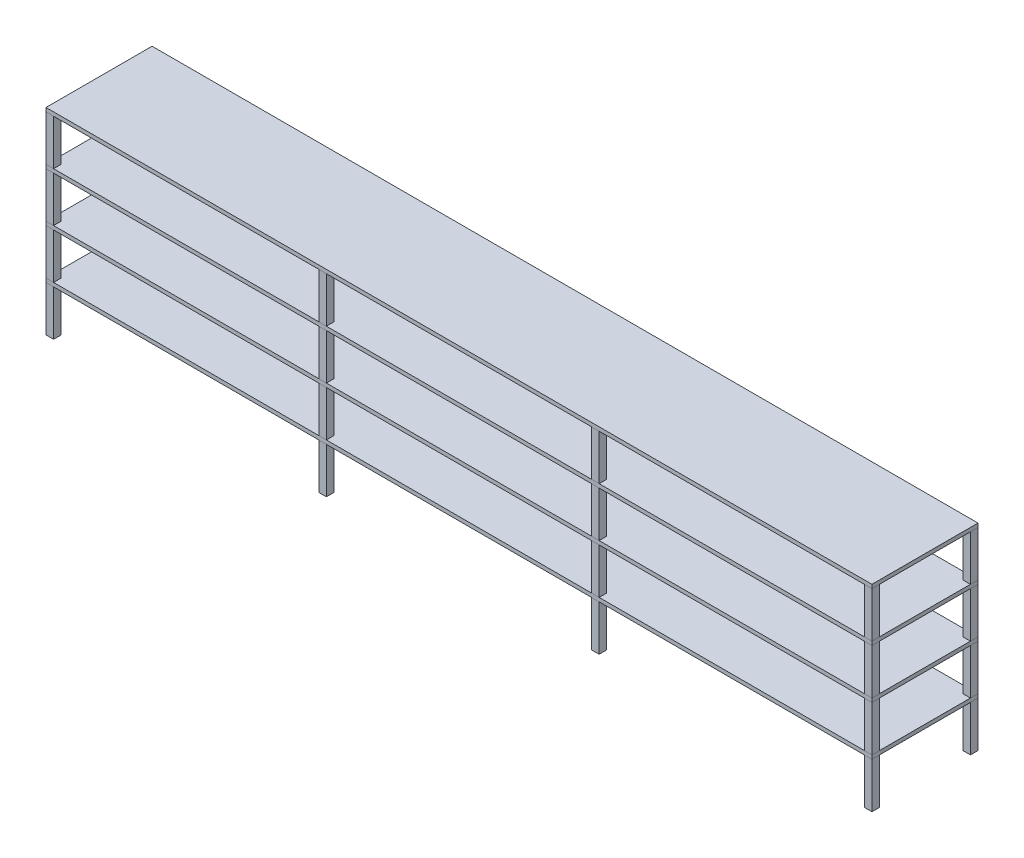
SolidWorks part; units mm, degrees
material "6061 Alloy"
ref_plane "Front Plane" through (0, 0, 0) normal (0, 0, 1) x (1, 0, 0)
ref_plane "Top Plane" through (0, 0, 0) normal (0, 1, 0) x (1, 0, 0)
ref_plane "Right Plane" through (0, 0, 0) normal (1, 0, 0) x (0, 0, -1)
sketch "Sketch1" plane through (0, 0, 0) normal (0, 1, 0) x (1, 0, 0)
  line L1 (-346.075, -44.45) -> (346.075, -44.45)
  line L2 (-346.075, -44.45) -> (-346.075, 44.45)
  line L3 (-346.075, 44.45) -> (346.075, 44.45)
  line L4 (346.075, -44.45) -> (346.075, 44.45)
  line L5 (-346.075, -44.45) -> (346.075, 44.45) construction
  line L6 (-346.075, 44.45) -> (346.075, -44.45) construction
  point P0 (0, 0)
  dimension "D1" = 88.9
  dimension "D2" = 692.15
sketch "Sketch2" plane through (0, 0, 0) normal (0, 1, 0) x (1, 0, 0)
  line L0 (-117.475, 44.45) -> (-117.475, 38.1)
  line L1 (-346.075, -44.45) -> (-339.725, -44.45)
  line L2 (-346.075, 44.45) -> (-339.725, 44.45)
  line L3 (-346.075, 44.45) -> (-346.075, 38.1)
  line L4 (-346.075, 38.1) -> (-339.725, 38.1)
  line L5 (-339.725, 44.45) -> (-339.725, 38.1)
  line L6 (-346.075, -44.45) -> (-346.075, -38.1)
  line L7 (-346.075, -38.1) -> (-339.725, -38.1)
  line L8 (-339.725, -44.45) -> (-339.725, -38.1)
  line L9 (-117.475, 44.45) -> (-111.125, 44.45)
  line L10 (-111.125, 44.45) -> (-111.125, 38.1)
  line L11 (-117.475, 38.1) -> (-111.125, 38.1)
  line L12 (-117.475, -38.1) -> (-111.125, -38.1)
  line L13 (-117.475, -44.45) -> (-117.475, -38.1)
  line L14 (-111.125, -44.45) -> (-111.125, -38.1)
  line L15 (-117.475, -44.45) -> (-111.125, -44.45)
  line L16 (111.125, 44.45) -> (111.125, 38.1)
  line L17 (111.125, 44.45) -> (117.475, 44.45)
  line L18 (117.475, 44.45) -> (117.475, 38.1)
  line L19 (111.125, 38.1) -> (117.475, 38.1)
  line L20 (111.125, -38.1) -> (117.475, -38.1)
  line L21 (111.125, -44.45) -> (111.125, -38.1)
  line L22 (117.475, -44.45) -> (117.475, -38.1)
  line L23 (111.125, -44.45) -> (117.475, -44.45)
  line L24 (339.725, 44.45) -> (339.725, 38.1)
  line L25 (339.725, 44.45) -> (346.075, 44.45)
  line L26 (346.075, 44.45) -> (346.075, 38.1)
  line L27 (339.725, 38.1) -> (346.075, 38.1)
  line L28 (339.725, -38.1) -> (346.075, -38.1)
  line L29 (339.725, -44.45) -> (339.725, -38.1)
  line L30 (346.075, -44.45) -> (346.075, -38.1)
  line L31 (339.725, -44.45) -> (346.075, -44.45)
  dimension "D1" = 6.35
extrude "Extrude1" add sketch "Sketch2" along normal blind 38.1
sketch "Sketch3" plane through (0, 38.1, 0) normal (0, 1, 0) x (1, 0, 0)
  line L1 (-346.075, 44.45) -> (346.075, 44.45)
  line L2 (-346.075, 44.45) -> (-346.075, -44.45)
  line L3 (-346.075, -44.45) -> (346.075, -44.45)
  line L4 (346.075, 44.45) -> (346.075, -44.45)
extrude "Extrude2" add sketch "Sketch3" along normal blind 3.175 separate body
pattern_linear "LPattern1" count 4 spacing 41.275 along (0, 1, 0) of bodies 102 101 104 103 106 105 109 108 107
